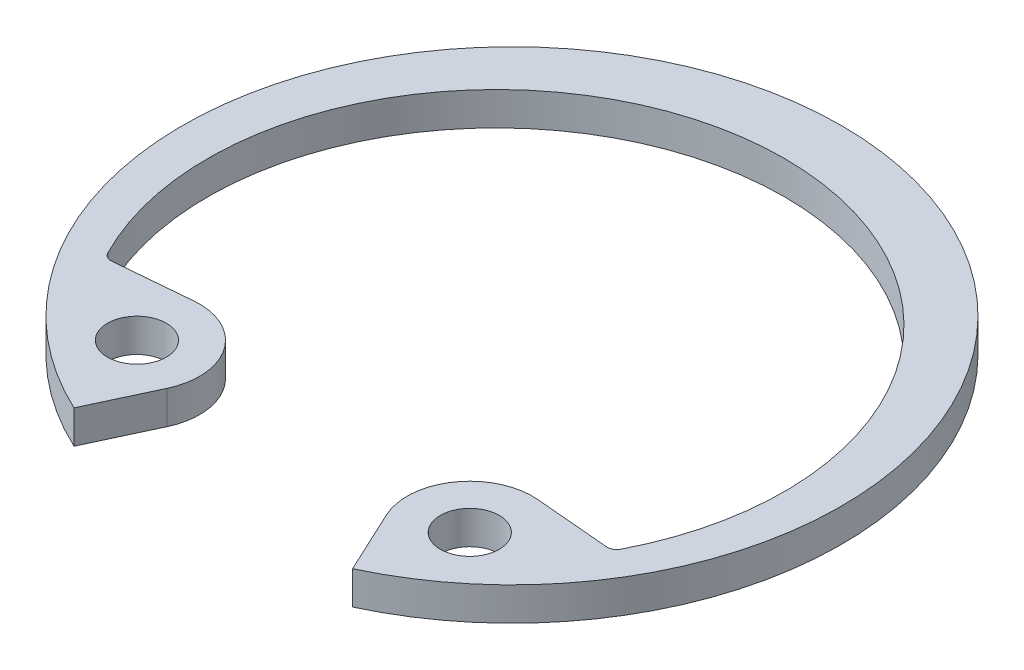
SolidWorks part; units mm, degrees
material "Cast Carbon Steel"
ref_plane "Front" through (0, 0, 0) normal (0, 0, 1) x (1, 0, 0)
ref_plane "Top" through (0, 0, 0) normal (0, 1, 0) x (1, 0, 0)
ref_plane "Right" through (0, 0, 0) normal (1, 0, 0) x (0, 0, -1)
sketch "Sketch2" plane through (0, 0, 0) normal (0, 1, 0) x (1, 0, 0)
  line L0 (0, 0) -> (0, -8.8138) construction
  line L1 (-6.7816, -4.1003) -> (-7.5423, -4.5603) construction
  line L2 (3.7249, -7.988) -> (2.932, -6.2877)
  line L3 (-3.7249, -7.988) -> (-2.932, -6.2877)
  line L4 (0, 7.2898) -> (0, 8.8138) construction
  line L5 (6.7816, -4.1003) -> (4.5975, -3.9092)
  line L6 (-6.7816, -4.1003) -> (-4.5975, -3.9092)
  line L7 (3.4058, -4.2688) -> (-1.3045, -8.0269) construction
  line L8 (-1.3045, -8.0269) -> (0.7865, -10.6478) construction
  line L9 (0.7865, -10.6478) -> (5.4969, -6.8897) construction
  line L10 (3.4058, -4.2688) -> (5.4969, -6.8897) construction
  line L11 (4.4513, -5.5792) -> (2.932, -6.2877) construction
  line L12 (4.4513, -5.5792) -> (5.4969, -6.8897) construction
  line L13 (3.4058, -4.2688) -> (-3.4058, -4.2688) construction
  line L14 (-3.4058, -4.2688) -> (-5.4969, -6.8897) construction
  line L15 (-8.8138, 0) -> (8.8138, 0) construction
  arc A1 (3.7249, -7.988) -> (-3.7249, -7.988) centre (0, 0) ccw
  arc A2 (6.7816, -4.1003) -> (-6.7816, -4.1003) centre (0, -0.4241) ccw
  circle A3 centre (0, 0) radius 8.8138 construction
  arc A4 (2.932, -6.2877) -> (4.5975, -3.9092) centre (4.4513, -5.5792) cw
  arc A5 (-2.932, -6.2877) -> (-4.5975, -3.9092) centre (-4.4513, -5.5792) ccw
  circle A6 centre (4.4513, -5.5792) radius 0.7874
  circle A7 centre (-4.4513, -5.5792) radius 0.7874
  arc A8 (6.7816, -4.1003) -> (-6.7816, -4.1003) centre (0, -0.4241) cw construction
  circle A9 centre (0, 0) radius 4.572 construction
  point P5 (4.4513, -5.5792)
  point P10 (3.4058, -4.2688)
  dimension "D1" = 60
  dimension "D2" = 60
  dimension "L" = 9.144
  dimension "R" = 1.5748
  dimension "Df" = 17.6276
  dimension "H" = 3.3528
  dimension "Angle" = 25
  dimension "Sec. Max" = 1.524
  dimension "Sec. Min" = 0.889
extrude "Extrude1" add sketch "Sketch2" against normal blind 0.889
fillet "Fillet1" radius 0.254 2 edges at (-6.7816, -0.4445, 4.1003) (6.7816, -0.4445, 4.1003)
move or copy body "Body-Move/Copy1" [suppressed] bodies to move or copy 116
move or copy body "Body-Move/Copy2" [suppressed] bodies to move or copy 116
